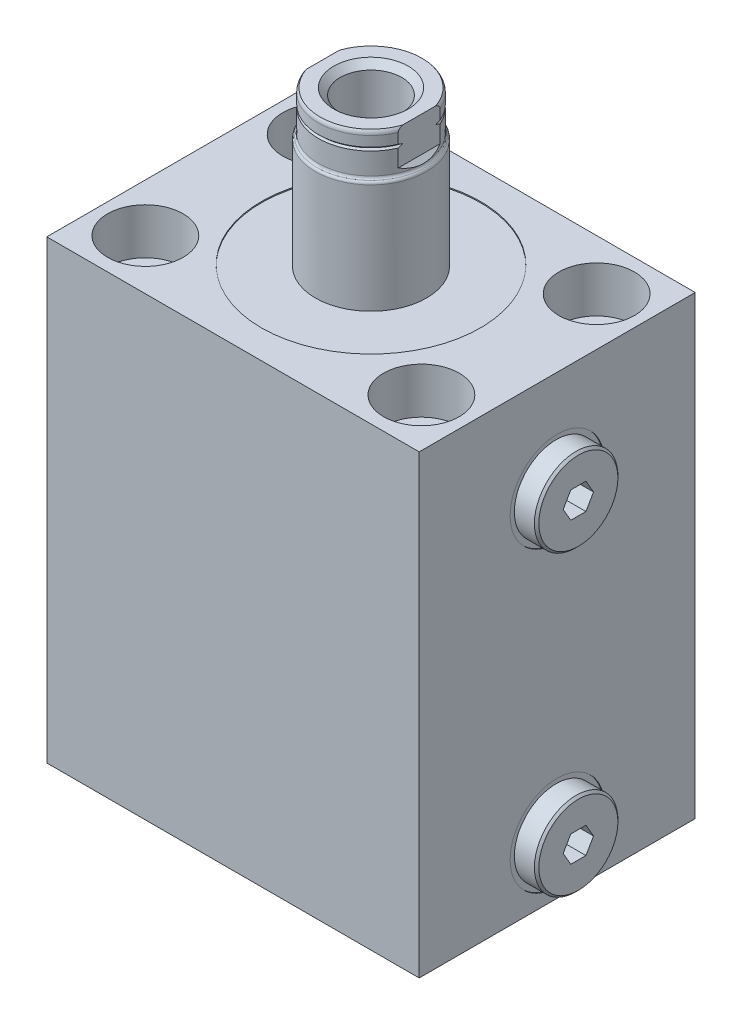
SolidWorks part; units mm, degrees
material "Alloy Steel"
ref_plane "Front Plane" through (0, 0, 0) normal (0, 0, 1) x (1, 0, 0)
ref_plane "Top Plane" through (0, 0, 0) normal (0, 1, 0) x (1, 0, 0)
ref_plane "Right Plane" through (0, 0, 0) normal (1, 0, 0) x (0, 0, -1)
sketch "Sketch1" plane through (0, 0, 0) normal (0, 1, 0) x (1, 0, 0)
  line L0 (-42.5, 31.5) -> (42.5, -31.5) construction
  line L1 (-42.5, 31.5) -> (42.5, 31.5)
  line L2 (-42.5, 31.5) -> (-42.5, -31.5)
  line L3 (-42.5, -31.5) -> (42.5, -31.5)
  line L4 (42.5, 31.5) -> (42.5, -31.5)
  point P4 (0, 0)
  dimension "D1" = 85
  dimension "D2" = 63
extrude "Extrude1" add sketch "Sketch1" along normal blind 104
sketch "Sketch2" plane through (0, 104, 0) normal (0, 1, 0) x (1, 0, 0)
  circle A0 centre (0, 0) radius 25
  dimension "D1" = 50
extrude "Cut-Extrude1" cut sketch "Sketch2" against normal blind 0.254
sketch "Sketch3" plane through (0, 0, 0) normal (0, 0, 1) x (1, 0, 0)
  line L0 (-6.848, 81) -> (35.4055, 81) construction
  line L1 (-42.5, 0) -> (42.5, 0) construction
  line L2 (42.5, 81) -> (42.5, 70.256)
  line L3 (42.5, 104) -> (42.5, 0) construction
  line L4 (42.5, 70.256) -> (42.246, 70.256)
  line L5 (42.246, 70.256) -> (42.246, 74.3452)
  line L6 (42.246, 74.3452) -> (41.5348, 75.0564)
  line L7 (41.5348, 75.0564) -> (26.752, 75.0564)
  line L8 (26.752, 75.0564) -> (26.752, 81)
  line L9 (26.752, 81) -> (42.5, 81)
  dimension "D1" = 81
  dimension "D2" = 21.488
  dimension "D3" = 0.254
  dimension "D4" = 11.8872
  dimension "D5" = 15.748
  dimension "D6" = 45
  dimension "D7" = 0.7112
revolve "Cut-Revolve1" cut sketch "Sketch3" angle 360 about L0
sketch "Sketch4" plane through (0, 0, 0) normal (0, 0, 1) x (1, 0, 0)
  line L0 (30.308, 81) -> (30.308, 86.9182)
  line L1 (41.5348, 81) -> (26.752, 81) construction
  line L2 (30.308, 86.9182) -> (42.246, 86.9182)
  line L3 (42.246, 86.9182) -> (42.246, 90.525)
  line L4 (42.246, 90.525) -> (47.326, 90.525)
  line L5 (47.326, 90.525) -> (47.326, 81)
  line L6 (47.326, 81) -> (30.308, 81)
  line L8 (42.246, 70.256) -> (42.246, 91.744) construction
  line L9 (8.7326, 81) -> (38.9701, 81) construction
  dimension "D1" = 11.938
  dimension "D2" = 11.8364
  dimension "D3" = 5.08
  dimension "D4" = 19.05
revolve "Revolve1" add sketch "Sketch4" angle 360 about L9
chamfer "Chamfer1" distance 0.508 angle 45 1 edges at (47.326, 81, 9.525)
sketch "Sketch5" plane through (47.326, 0, 0) normal (1, 0, 0) x (0, 0, -1)
  line L1 (1.7304, 83.9972) -> (-1.7304, 83.9972)
  line L2 (-1.7304, 83.9972) -> (-3.4609, 81)
  line L3 (-3.4609, 81) -> (-1.7304, 78.0028)
  line L4 (-1.7304, 78.0028) -> (1.7304, 78.0028)
  line L5 (1.7304, 78.0028) -> (3.4609, 81)
  line L6 (3.4609, 81) -> (1.7304, 83.9972)
  circle A0 centre (0, 81) radius 2.9972 construction
  dimension "D1" = 5.9944
extrude "Cut-Extrude2" cut sketch "Sketch5" against normal blind 5.9944
pattern_linear "LPattern1" count 2 spacing 68 along (0, -1, 0) of "Cut-Revolve1", "Revolve1", "Chamfer1", "Cut-Extrude2"
sketch "Sketch6" plane through (0, 0, 0) normal (0, 0, 1) x (1, 0, 0)
  line L0 (-42.5, 0) -> (42.5, 0) construction
  line L1 (0, 0) -> (0, 18.7888) construction
  line L12 (0, 0) -> (0, 14.8958)
  line L13 (5.7025, 0) -> (0, 0)
  line L14 (1.2446, 14.148) -> (0, 14.8958)
  line L15 (1.2446, 4.9529) -> (1.2446, 14.148)
  line L16 (1.7525, 4.445) -> (1.2446, 4.9529)
  line L17 (3.2512, 4.445) -> (1.7525, 4.445)
  line L18 (3.2512, 1.448) -> (3.2512, 4.445)
  line L19 (5.7025, 1.448) -> (3.2512, 1.448)
  line L20 (5.7025, 0) -> (5.7025, 1.448)
  dimension "D1" = 59
  dimension "D2" = 14.8958
  dimension "D3" = 2.4892
  dimension "D4" = 11.405
  dimension "D5" = 1.448
  dimension "D6" = 6.5024
  dimension "D7" = 4.445
  dimension "D8" = 45
  dimension "D9" = 0.5079
revolve "Cut-Revolve2" cut sketch "Sketch6" angle 360 about L1
sketch "Sketch7" plane through (0, 0, 0) normal (0, 0, 1) x (1, 0, 0)
  line L0 (0, 0) -> (0, 17.946) construction
  line L1 (0, 14.148) -> (0, 14.8958) construction
  line L2 (-42.5, 0) -> (42.5, 0) construction
  circle A0 centre (4.814, 0.5844) radius 0.889
  dimension "D1" = 9.628
  dimension "D2" = 1.778
  dimension "D3" = 0.5844
revolve "Revolve3" add sketch "Sketch7" angle 360 about L0
pattern_linear "LPattern2" count 2 spacing 31.5 along (-1, 0, 0) of "Cut-Revolve2", "Revolve3"
sketch "Sketch8" plane through (0, 0, 0) normal (0, 0, 1) x (1, 0, 0)
  line L0 (12.6875, 103.746) -> (12.6875, 128.7261)
  line L1 (11.6341, 139) -> (0, 139)
  line L2 (0, 139) -> (0, 103.746)
  line L3 (12, 138.0094) -> (12, 130)
  line L4 (12.6875, 103.746) -> (0, 103.746)
  line L5 (0, 0) -> (0, 83.6966) construction
  line L6 (25, 103.746) -> (-25, 103.746) construction
  line L7 (-42.5, 0) -> (42.5, 0) construction
  arc A0 (12, 138.0094) -> (11.6341, 139) centre (10.476, 138.0094) ccw
  arc A1 (12, 130) -> (12.3438, 129.363) centre (12.762, 130) ccw
  arc A2 (12.6875, 128.7261) -> (12.3438, 129.363) centre (11.9255, 128.7261) ccw
  dimension "D1" = 1.524
  dimension "D7" = 0.762
  dimension "D8" = 0.762
  dimension "D2" = 9
  dimension "D3" = 139
  dimension "D4" = 0.9906
  dimension "D5" = 24
  dimension "D6" = 25.375
revolve "Revolve4" add sketch "Sketch8" angle 360 about L5
sketch "Sketch10" plane through (0, 0, 0) normal (0, 0, 1) x (1, 0, 0)
  line L0 (8.5, 139) -> (7.0105, 137.5105)
  line L1 (7.0105, 137.5105) -> (7.0105, 109.03)
  line L2 (7.0105, 109.03) -> (0, 104.8177)
  line L3 (0, 104.8177) -> (0, 139)
  line L4 (0, 139) -> (8.5, 139)
  line L5 (0, 139) -> (0, 82.7828) construction
  line L6 (11.6341, 139) -> (-11.6341, 139) construction
  dimension "D1" = 45
  dimension "D2" = 1.4895
  dimension "D3" = 14.021
  dimension "D4" = 59
  dimension "D5" = 29.97
revolve "Cut-Revolve3" cut sketch "Sketch10" angle 360 about L5
sketch "Sketch11" plane through (0, 0, 0) normal (0, 0, 1) x (1, 0, 0)
  line L0 (12, 135.698) -> (11.619, 135.317)
  line L1 (11.619, 135.317) -> (12, 134.936)
  line L2 (12, 134.936) -> (12, 135.698)
  line L3 (12, 130) -> (12, 138.0094) construction
  line L4 (11.619, 135.317) -> (12, 135.317) construction
  line L5 (11.6341, 139) -> (-11.6341, 139) construction
  line L6 (0, 0) -> (0, 94.5745) construction
  dimension "D1" = 0.762
  dimension "D2" = 3.683
  dimension "D3" = 90
revolve "Cut-Revolve4" cut sketch "Sketch11" angle 360 about L6
sketch "Sketch12" plane through (0, 0, 0) normal (0, 0, 1) x (1, 0, 0)
  line L0 (0, 0) -> (0, 87.4273) construction
  line L1 (11, 139) -> (11, 131)
  line L2 (8.5, 139) -> (-8.5, 139) construction
  line L3 (11, 131) -> (12.6875, 129.3125)
  line L4 (12.6875, 129.3125) -> (12.6875, 139)
  line L5 (12.6875, 139) -> (11, 139)
  line L6 (12.6875, 103.746) -> (12.6875, 128.7261) construction
  line L7 (-12.6875, 139) -> (-11, 139)
  line L8 (-12.6875, 129.3125) -> (-12.6875, 139)
  line L9 (-11, 131) -> (-12.6875, 129.3125)
  line L10 (-11, 139) -> (-11, 131)
  dimension "D1" = 22
  dimension "D2" = 45
  dimension "D3" = 8
extrude "Cut-Extrude3" cut sketch "Sketch12" against normal through all and the other way through all
hole_wizard "Hole1" positions "Sketch14" profile "Sketch13" legacy end condition through all
sketch "Sketch14" plane through (0, 104, 0) normal (0, 1, 0) x (-1, 0, 0)
  line L0 (0, 0) -> (0, 30.0241) construction
  line L1 (0, 0) -> (32.2854, 0) construction
  point P0 (31.5, 20)
  point P10 (31.5, -20)
  point P12 (-31.5, -20)
  point P13 (-31.5, 20)
  dimension "D1" = 40
  dimension "D2" = 63
sketch "Sketch13" plane through (-31.5, 104, 20) normal (1, 0, 0) x (0, 0, 1)
  line L0 (0, 0) -> (0, 104.3046)
  line L1 (0, 104.3046) -> (5.245, 104.3046)
  line L2 (5.245, 104.3046) -> (5.245, 10.49)
  line L3 (5.245, 10.49) -> (8.6235, 10.49)
  line L4 (8.6235, 10.49) -> (8.6235, 0)
  line L5 (8.6235, 0) -> (0, 0)
  line L6 (0, 110) -> (0, -10) construction
  dimension "Diameter" = 10.49
  dimension "Depth" = 104.3046
  dimension "C-Bore Diameter" = 17.247
  dimension "C-Bore Depth" = 10.49
